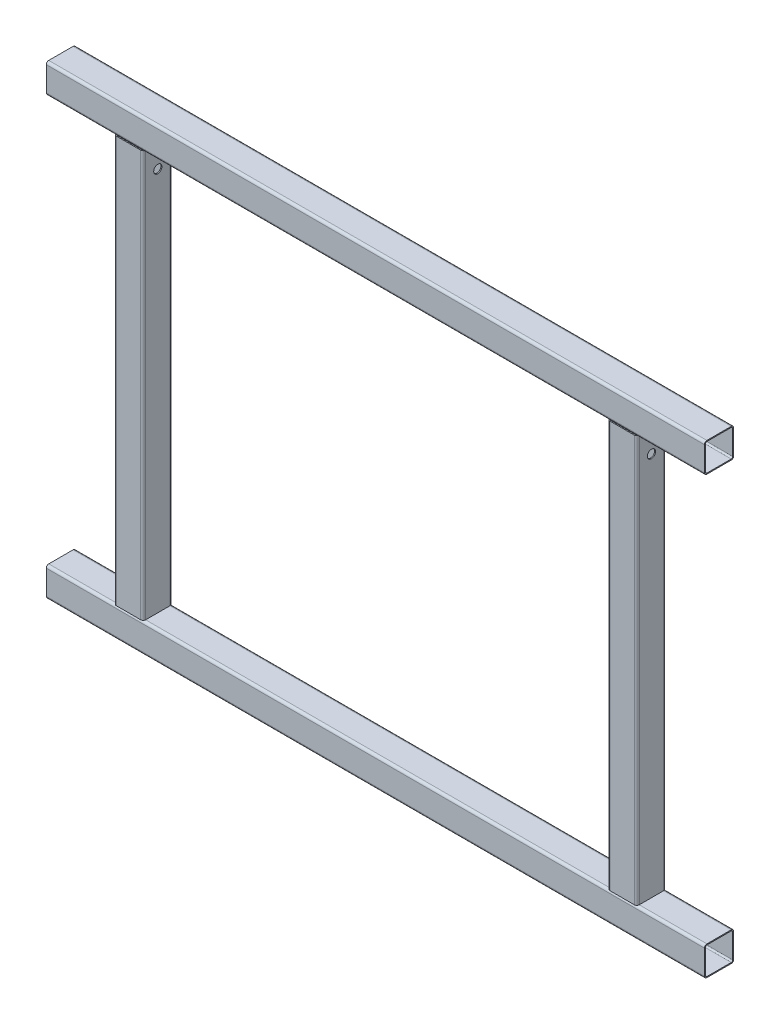
SolidWorks part; units mm, degrees
ref_plane "Front Plane" through (0, 0, 0) normal (0, 0, 1) x (1, 0, 0)
ref_plane "Top Plane" through (0, 0, 0) normal (0, 1, 0) x (1, 0, 0)
ref_plane "Right Plane" through (0, 0, 0) normal (1, 0, 0) x (0, 0, -1)
sketch "Sketch1" plane through (0, 0, 0) normal (0, 0, 1) x (1, 0, 0)
  line L0 (-400, 0) -> (400, 0)
  line L1 (-400, 530) -> (400, 530)
  line L2 (0, 0) -> (0, 577.75) construction
  line L3 (-300, 530) -> (-300, 0)
  line L4 (300, 530) -> (300, 0)
  point P11 (0, 530)
  dimension "D1" = 800
  dimension "D2" = 600
  dimension "D3" = 530
other "Structural Member1"
ref_plane "Plane1" through (-400, 530, 0) normal (1, 0, 0) x (0, 1, 0)
sketch "Sketch11" plane through (-400, 530, 0) normal (1, 0, 0) x (0, 1, 0)
  line L1 (-14.8, -17.8) -> (14.8, -17.8)
  line L2 (-17.8, -14.8) -> (-17.8, 14.8)
  line L3 (-14.8, 17.8) -> (14.8, 17.8)
  line L4 (17.8, -14.8) -> (17.8, 14.8)
  line L5 (-17.8, -17.8) -> (17.8, 17.8) construction
  line L6 (-17.8, 17.8) -> (17.8, -17.8) construction
  line L7 (-14.8, 16.6) -> (14.8, 16.6)
  line L8 (-16.6, 14.8) -> (-16.6, -14.8)
  line L9 (-14.8, -16.6) -> (14.8, -16.6)
  line L10 (16.6, 14.8) -> (16.6, -14.8)
  line L11 (-16.6, 16.6) -> (16.6, -16.6) construction
  line L12 (-16.6, -16.6) -> (16.6, 16.6) construction
  arc A0 (14.8, 17.8) -> (17.8, 14.8) centre (14.8, 14.8) cw
  arc A1 (14.8, -17.8) -> (17.8, -14.8) centre (14.8, -14.8) ccw
  arc A2 (-14.8, -17.8) -> (-17.8, -14.8) centre (-14.8, -14.8) cw
  arc A3 (-17.8, 14.8) -> (-14.8, 17.8) centre (-14.8, 14.8) cw
  arc A4 (-16.6, -14.8) -> (-14.8, -16.6) centre (-14.8, -14.8) ccw
  arc A5 (14.8, -16.6) -> (16.6, -14.8) centre (14.8, -14.8) ccw
  arc A6 (14.8, 16.6) -> (16.6, 14.8) centre (14.8, 14.8) cw
  arc A7 (-14.8, 16.6) -> (-16.6, 14.8) centre (-14.8, 14.8) ccw
  point P0 (0, 0)
  point P5 (0, 0)
  point P35 (0, 0)
  dimension "D4" = 3
  dimension "D5" = 1.8
  dimension "D1" = 35.6
  dimension "D2" = 35.6
  dimension "D3" = 1.2
sketch "Sketch12" plane through (0, 0, 0) normal (1, 0, 0) x (0, 0, -1)
  line L0 (0, 530) -> (0, 0) construction
  circle A0 centre (0, 485) radius 5
  dimension "D1" = 10
  dimension "D2" = 485
extrude "Cut-Extrude1" cut sketch "Sketch12" against normal through all and the other way through all
